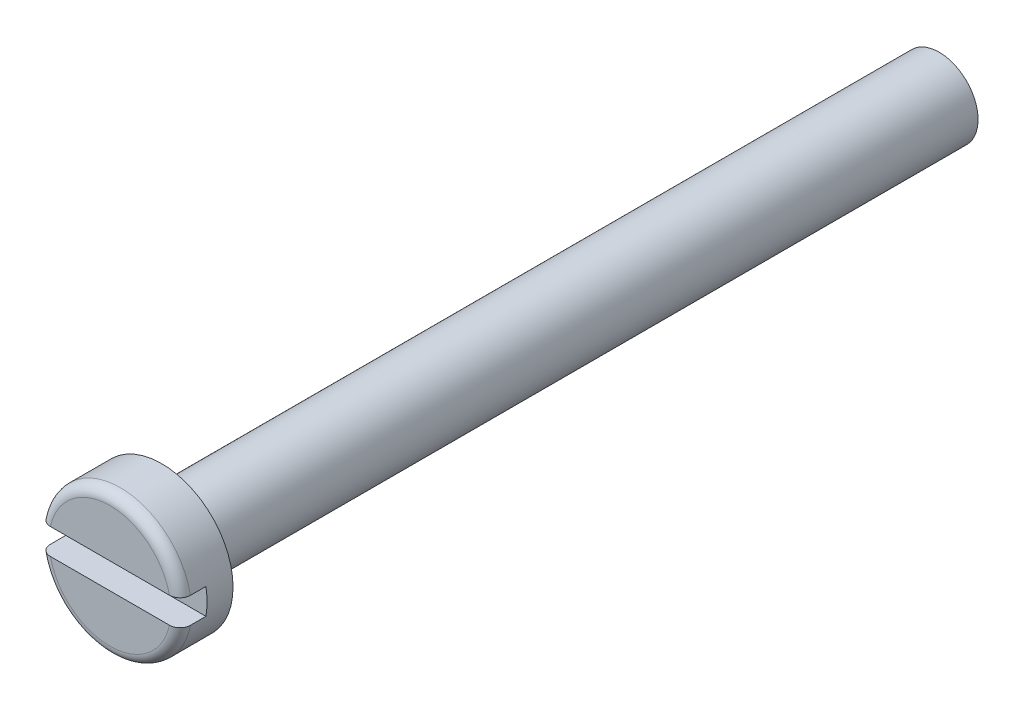
SolidWorks part; units mm, degrees
ref_plane "Front Plane" through (0, 0, 0) normal (0, 0, 1) x (1, 0, 0)
ref_plane "Top Plane" through (0, 0, 0) normal (0, 1, 0) x (1, 0, 0)
ref_plane "Right Plane" through (0, 0, 0) normal (1, 0, 0) x (0, 0, -1)
sketch "Sketch1" plane through (0, 0, 0) normal (0, 0, 1) x (1, 0, 0)
  circle A0 centre (0, 0) radius 2.75
  dimension "D1" = 5.5
extrude "Boss-Extrude1" add sketch "Sketch1" along normal blind 2
fillet "Fillet1" radius 0.4 1 edges at (2.75, 0, 2)
sketch "Sketch2" plane through (0, 0, 2) normal (0, 0, 1) x (1, 0, 0)
  line L1 (-3.9255, -0.5) -> (3.9255, -0.5)
  line L2 (-3.9255, -0.5) -> (-3.9255, 0.5)
  line L3 (-3.9255, 0.5) -> (3.9255, 0.5)
  line L4 (3.9255, -0.5) -> (3.9255, 0.5)
  line L5 (-3.9255, -0.5) -> (3.9255, 0.5) construction
  line L6 (-3.9255, 0.5) -> (3.9255, -0.5) construction
  point P0 (0, 0)
  dimension "D1" = 1
extrude "Cut-Extrude1" cut sketch "Sketch2" against normal blind 1
sketch "Sketch3" plane through (0, 0, 0) normal (0, 0, -1) x (-1, 0, 0)
  circle A0 centre (0, 0) radius 1.5
  dimension "D1" = 3
extrude "Boss-Extrude2" add sketch "Sketch3" along normal blind 30
